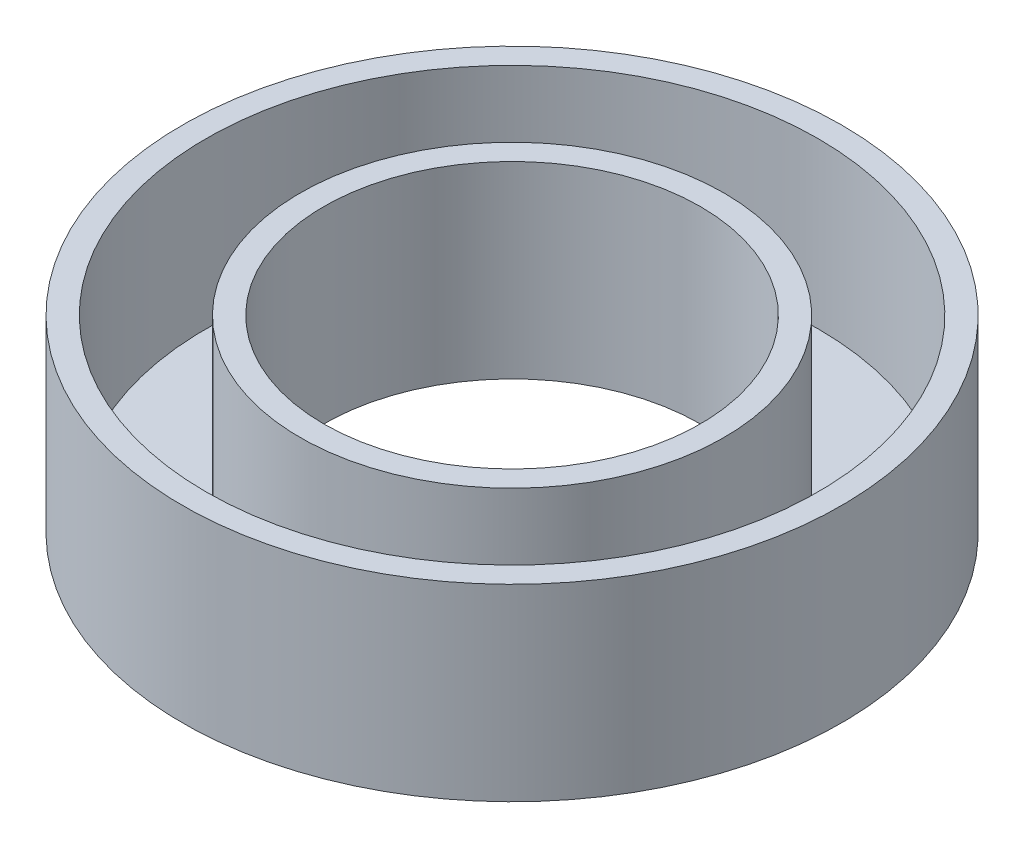
SolidWorks part; units mm, degrees
material "BUNA N"
ref_plane "Front" through (0, 0, 0) normal (0, 0, 1) x (1, 0, 0)
ref_plane "Top" through (0, 0, 0) normal (0, 1, 0) x (1, 0, 0)
ref_plane "Right" through (0, 0, 0) normal (1, 0, 0) x (0, 0, -1)
sketch "Sketch1" plane through (0, 0, 0) normal (0, 0, 1) x (1, 0, 0)
  line L0 (-11.1125, 6.35) -> (-11.1125, 0)
  line L1 (-11.1125, 0) -> (-6.35, 0)
  line L2 (-6.35, 0) -> (-6.35, 6.35)
  line L3 (-6.35, 6.35) -> (-7.1437, 6.35)
  line L4 (-7.1437, 6.35) -> (-7.1437, 0.7938)
  line L5 (-7.1437, 0.7938) -> (-10.3187, 0.7937)
  line L6 (-10.3187, 0.7937) -> (-10.3187, 6.35)
  line L7 (-10.3187, 6.35) -> (-11.1125, 6.35)
  line L8 (0, 0) -> (0, 6.35) construction
  dimension "D1" = 11.1125
  dimension "D2" = 6.35
  dimension "D3" = 6.35
  dimension "D4" = 0.7937
  dimension "D5" = 0.7937
revolve "Revolve1" add sketch "Sketch1" angle 360 about L8
equation "\"D5@Sketch1\"=\"D4@Sketch1\""
